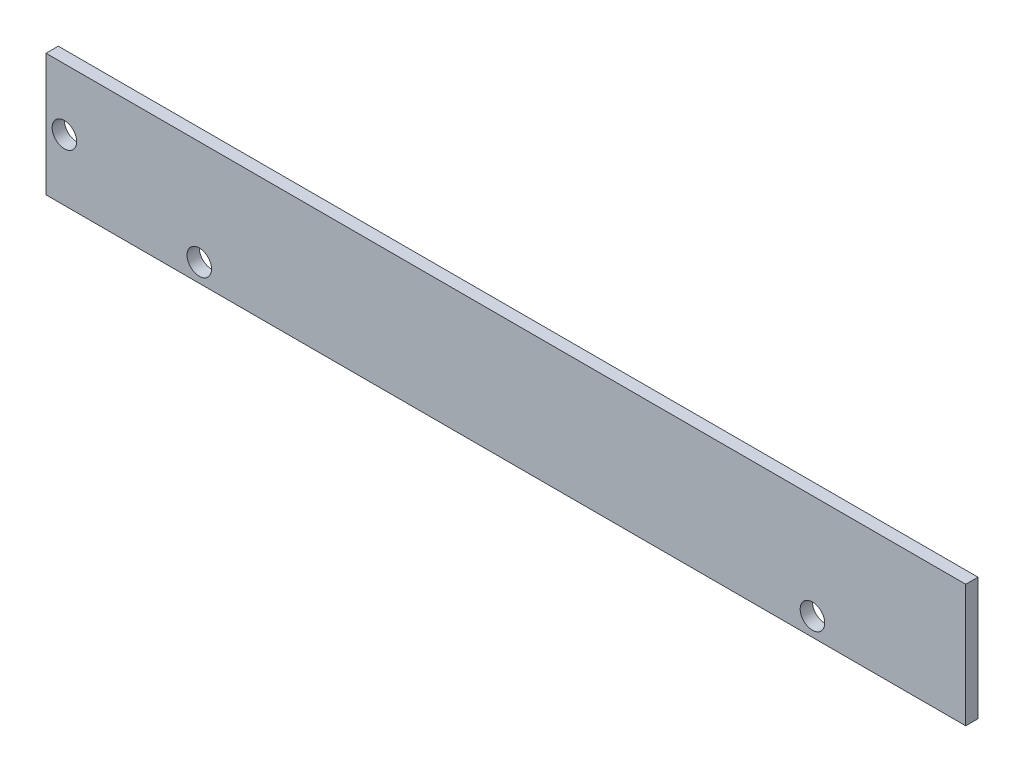
SolidWorks part; units mm, degrees
ref_plane "前视基准面" through (0, 0, 0) normal (0, 0, 1) x (1, 0, 0)
ref_plane "上视基准面" through (0, 0, 0) normal (0, 1, 0) x (1, 0, 0)
ref_plane "右视基准面" through (0, 0, 0) normal (1, 0, 0) x (0, 0, -1)
sketch "草图1" plane through (0, 0, 0) normal (0, 0, 1) x (1, 0, 0)
  line L0 (-50, -10) -> (-50, -7)
  line L1 (-75, 10) -> (75, 10)
  line L2 (-75, 10) -> (-75, -10)
  line L3 (-75, -10) -> (75, -10)
  line L4 (75, 10) -> (75, -10)
  line L5 (-75, 0) -> (-72, 0)
  line L6 (50, -10) -> (50, -7)
  circle A0 centre (-50, -7) radius 2
  circle A1 centre (50, -7) radius 2
  circle A2 centre (-72, 0) radius 2
  point P0 (0, 0)
  point P6 (-50, -10)
  point P7 (50, -10)
  dimension "D7" = 3
  dimension "D1" = 150
  dimension "D2" = 20
  dimension "D3" = 25
  dimension "D4" = 25
  dimension "D5" = 3
  dimension "D6" = 3
extrude "凸台-拉伸2" add sketch "草图1" along normal blind 2
ref_plane "基准面1" through (0, 0, 0) normal (0, 1, 0) x (-1, 0, 0)
